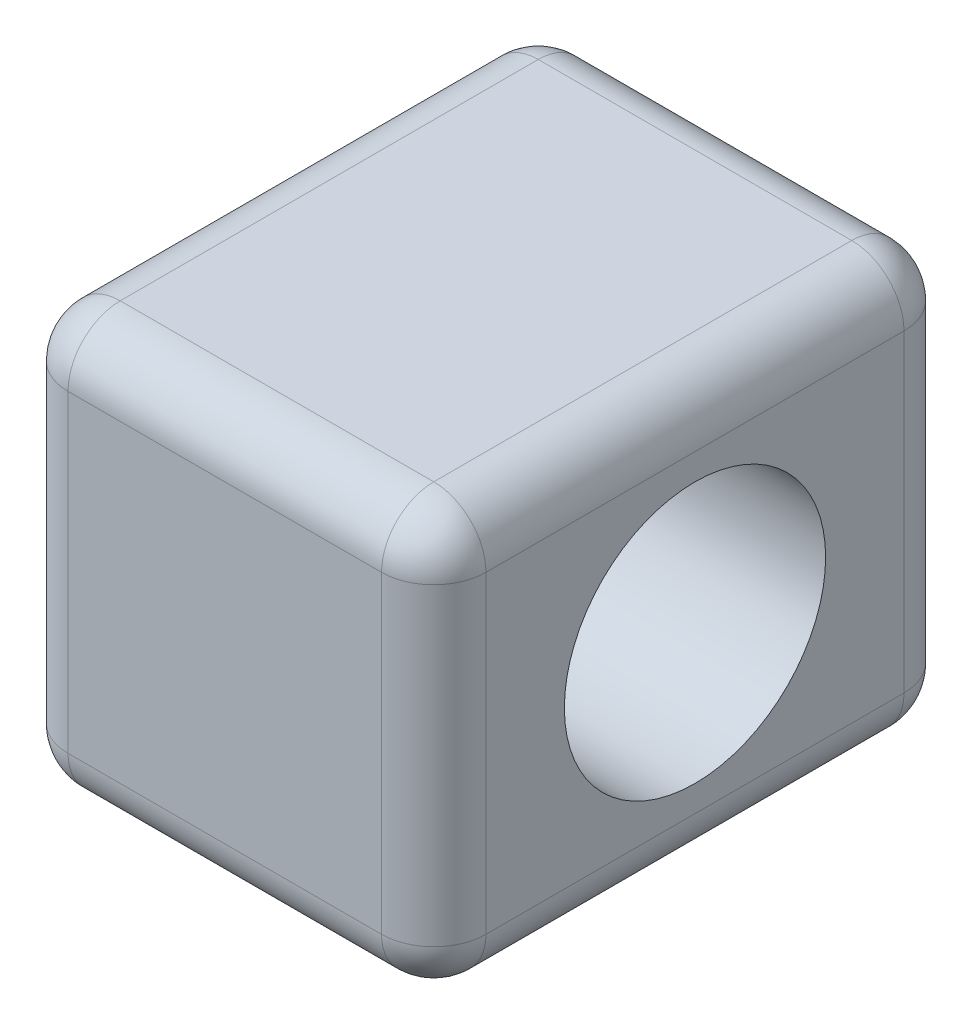
SolidWorks part; units mm, degrees
material "ABS"
ref_plane "前视基准面" through (0, 0, 0) normal (0, 0, 1) x (1, 0, 0)
ref_plane "上视基准面" through (0, 0, 0) normal (0, 1, 0) x (1, 0, 0)
ref_plane "右视基准面" through (0, 0, 0) normal (1, 0, 0) x (0, 0, -1)
other "Configuration Table"
sketch "草图1" plane through (0, 0, 0) normal (0, 0, 1) x (1, 0, 0)
  line L1 (0, 8) -> (8, 8)
  line L2 (0, 8) -> (0, 0)
  line L3 (0, 0) -> (8, 0)
  line L4 (8, 8) -> (8, 0)
  dimension "D1" = 8
  dimension "D2" = 8
extrude "凸台-拉伸1" add sketch "草图1" along normal blind 10
sketch "草图4" plane through (8, 0, 0) normal (1, 0, 0) x (0, 0, -1)
  line L0 (-10, 4) -> (0, 4) construction
  line L1 (-10, 0) -> (-10, 8) construction
  line L2 (0, 0) -> (0, 8) construction
  circle A0 centre (-5, 4) radius 2.5
  dimension "D1" = 5
  dimension "D2" = 5
extrude "切除-拉伸2" cut sketch "草图4" against normal through all
fillet "圆角1" radius 1 12 edges at (0, 0, 5) (8, 0, 5) (8, 4, 10) (4, 0, 10) (0, 4, 10) (8, 8, 5) (4, 8, 10) (0, 8, 5) (4, 0, 0) (8, 4, 0) (4, 8, 0) (0, 4, 0)
